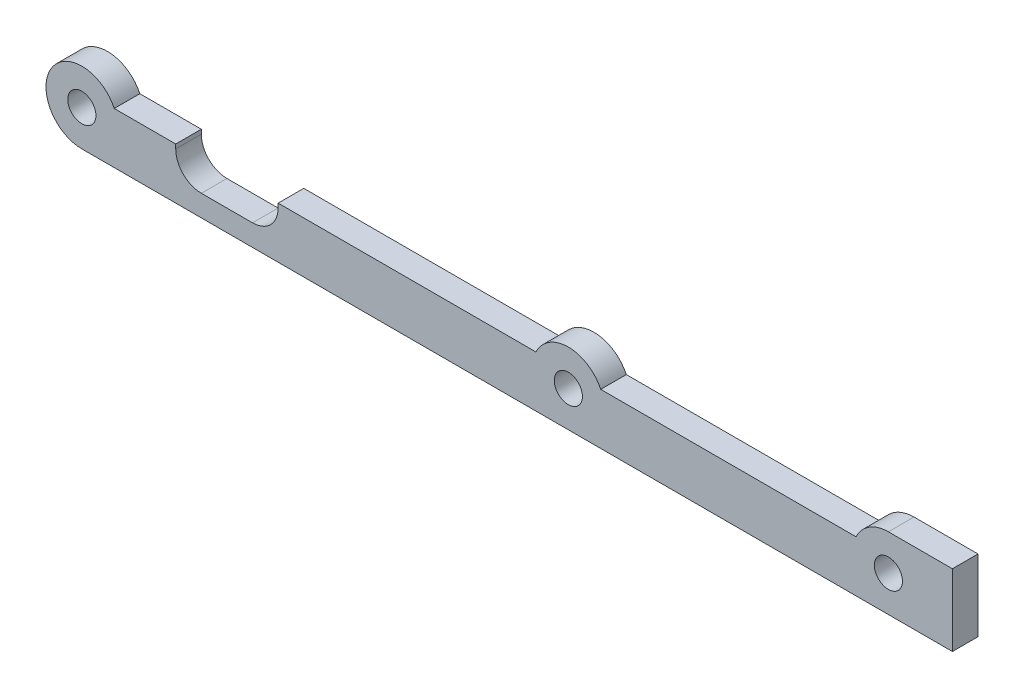
SolidWorks part; units mm, degrees
material "6061-T6 Black anodised"
ref_plane "Front Plane" through (0, 0, 0) normal (0, 0, 1) x (1, 0, 0)
ref_plane "Top Plane" through (0, 0, 0) normal (0, 1, 0) x (1, 0, 0)
ref_plane "Right Plane" through (0, 0, 0) normal (1, 0, 0) x (0, 0, -1)
sketch "Sketch1" plane through (0, 0, 0) normal (0, 0, 1) x (1, 0, 0)
  line L0 (-53.2053, 1.8) -> (-46, 1.8)
  line L1 (-57, -4.2) -> (45, -4.2)
  line L2 (-46, -1.7) -> (-34, -1.7)
  line L3 (37.5, 4.2) -> (45, 4.2)
  line L4 (45, -4.2) -> (45, 4.2)
  line L5 (-34, -1.7) -> (-34, 1.8)
  line L6 (-34, 1.8) -> (-3.7947, 1.8)
  line L7 (-46, 1.8) -> (-46, -1.7)
  line L9 (3.7947, 1.8) -> (33.7053, 1.8)
  circle A0 centre (0, 0) radius 1.65
  circle A1 centre (-57, 0) radius 1.65
  circle A2 centre (37.5, 0) radius 1.65
  arc A3 (-57, -4.2) -> (-53.2053, 1.8) centre (-57, 0) cw
  arc A4 (37.5, 4.2) -> (33.7053, 1.8) centre (37.5, 0) ccw
  arc A6 (3.7947, 1.8) -> (-3.7947, 1.8) centre (0, 0) ccw
  dimension "D2" = 37.5
  dimension "D3" = 3.3
  dimension "D1" = 57
  dimension "D4" = 4.2
  dimension "D5" = 7.5
  dimension "D6" = 6
  dimension "D7" = 2.5
  dimension "D8" = 11
  dimension "D9" = 12
extrude "Boss-Extrude1" add sketch "Sketch1" along normal blind 3
fillet "Fillet1" radius 3 2 edges at (-34, -1.7, 1.5) (-46, -1.7, 1.5)
